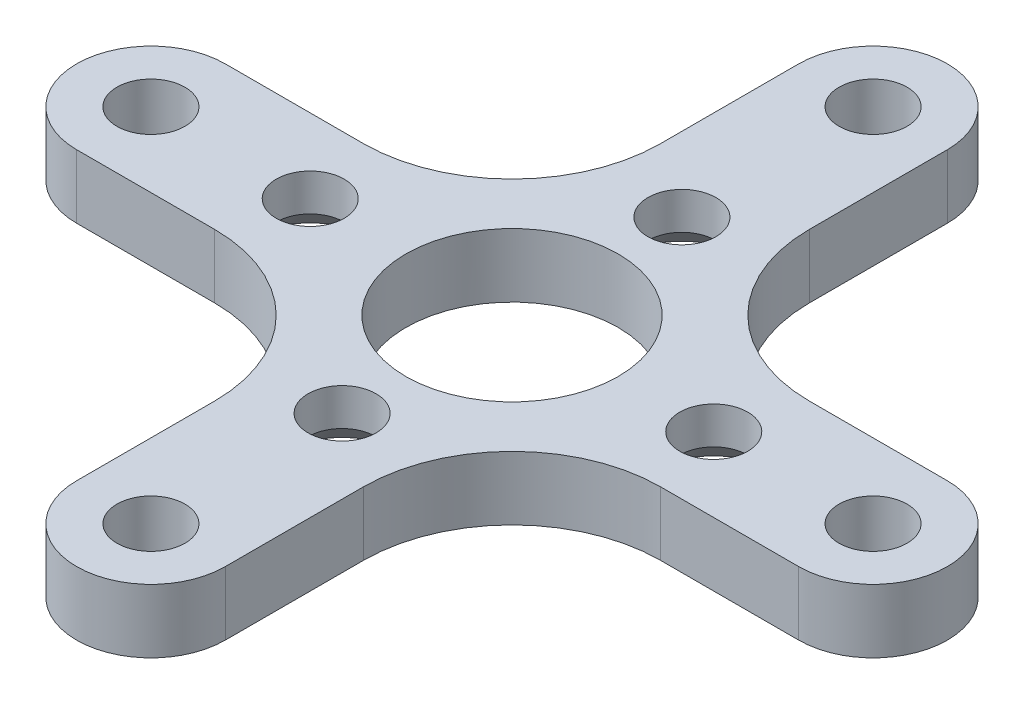
SolidWorks part; units mm, degrees
ref_plane "Front Plane" through (0, 0, 0) normal (0, 0, 1) x (1, 0, 0)
ref_plane "Top Plane" through (0, 0, 0) normal (0, 1, 0) x (1, 0, 0)
ref_plane "Right Plane" through (0, 0, 0) normal (1, 0, 0) x (0, 0, -1)
sketch "Sketch1" plane through (0, 0, 0) normal (0, 1, 0) x (1, 0, 0)
  line L0 (0, 69.7418) -> (0, -61.909) construction
  line L2 (3.5, -17) -> (3.5, -10.5)
  line L4 (-3.5, -17) -> (-3.5, -10.5)
  line L5 (-66.5785, 0) -> (62.9634, 0) construction
  line L6 (-3.5, 10.5) -> (-3.5, 17)
  line L7 (-17, 3.5) -> (-10.5, 3.5)
  line L9 (-17, -3.5) -> (-10.5, -3.5)
  line L11 (10.5, -3.5) -> (17, -3.5)
  line L12 (3.5, 10.5) -> (3.5, 17)
  line L13 (10.5, 3.5) -> (17, 3.5)
  arc A10 (-3.5, 10.5) -> (-10.5, 3.5) centre (-10.5, 10.5) cw
  arc A11 (-3.5, -10.5) -> (-10.5, -3.5) centre (-10.5, -10.5) ccw
  arc A12 (10.5, 3.5) -> (3.5, 10.5) centre (10.5, 10.5) cw
  arc A13 (3.5, -10.5) -> (10.5, -3.5) centre (10.5, -10.5) cw
  arc A15 (-16.6397, 3.4814) -> (-16.6397, -3.4814) centre (-17, 0) ccw
  arc A16 (3.4814, 16.6397) -> (-3.4814, 16.6397) centre (0, 17) ccw
  arc A17 (16.6397, -3.4814) -> (16.6397, 3.4814) centre (17, 0) ccw
  arc A18 (-3.4814, -16.6397) -> (3.4814, -16.6397) centre (0, -17) ccw
  point P30 (0, 0)
  point P61 (0, 0)
  dimension "D10" = 7
  dimension "D11" = 7
  dimension "D12" = 7
  dimension "D13" = 7
  dimension "D15" = 4
extrude "Boss-Extrude1" add sketch "Sketch1" along normal blind 3
sketch "Sketch2" plane through (0, 0, 0) normal (0, -1, 0) x (1, 0, 0)
  line L0 (20.5, 0) -> (-20.5, 0) construction
  line L1 (0, -20.5) -> (0, 20.5) construction
  arc A0 (-17, 3.5) -> (-17, -3.5) centre (-17, 0) ccw construction
  arc A1 (17, -3.5) -> (17, 3.5) centre (17, 0) ccw construction
  arc A2 (-3.5, -17) -> (3.5, -17) centre (0, -17) ccw construction
  arc A3 (3.5, 17) -> (-3.5, 17) centre (0, 17) ccw construction
  circle A4 centre (0, 0) radius 17 construction
  dimension "D1" = 34
hole_wizard "Ø10.0 (10) Diameter Hole1" positions "3DSketch4" profile "Sketch5" hole size "Ø10.0" standard "ISO"
sketch3d "3DSketch4"
  point P0 (0, 0, 0)
  point P3 (0, 0, 0)
sketch "Sketch5" plane through (0, 0, 0) normal (1, 0, 0) x (0, 0, -1)
  line L0 (0, 0) -> (0, 13.0043)
  line L1 (0, 13.0043) -> (5, 10)
  line L2 (5, 10) -> (5, 0)
  line L5 (5, 0) -> (0, 0)
  line L10 (0, 13.0043) -> (-5, 10) construction
  line L11 (0, -6.35) -> (0, 107.95) construction
  dimension "Hole Dia." = 10
  dimension "Hole Depth" = 10
  dimension "Drill Angle" = 118
hole_wizard "Ø3.2 (3.2) Diameter Hole3" positions "3DSketch7" profile "Sketch8" hole size "Ø3.2" standard "ISO"
sketch3d "3DSketch7"
  line L0 (0, 0, -20.5) -> (0, 0, 20.5) construction
  circle A0 centre (0, 0, 0) radius 17 construction
  point P0 (0, 0, 17)
  point P6 (0, -17, 0)
sketch "Sketch8" plane through (0, 0, 17) normal (1, 0, 0) x (0, 0, -1)
  line L0 (0, 0) -> (0, 10.9614)
  line L1 (0, 10.9614) -> (1.6, 10)
  line L2 (1.6, 10) -> (1.6, 0)
  line L5 (1.6, 0) -> (0, 0)
  line L10 (0, 10.9614) -> (-1.6, 10) construction
  line L11 (0, -6.35) -> (0, 107.95) construction
  dimension "Hole Dia." = 3.2
  dimension "Hole Depth" = 10
  dimension "Drill Angle" = 118
pattern_circular "CirPattern1" count 4 over 360 about axis through (0, 0, 0) along (0, 1, 0) of "Ø3.2 (3.2) Diameter Hole3"
hole_wizard "CSK for M3 Flat Head Machine Screw1" positions "3DSketch8" profile "Sketch9" countersink size "M3" standard "ANSI Metric" end condition through all
sketch3d "3DSketch8"
  line L0 (0, 0, -20.5) -> (0, 0, 20.5) construction
  line L1 (20.5, 0, 0) -> (-20.5, 0, 0) construction
  point P0 (0, 0, -8)
  point P4 (0, 0, 8)
  point P6 (-9.5, 0, 0)
  point P10 (9.5, 0, 0)
  dimension "D1" = 16
  dimension "D2" = 8
  dimension "D3" = 19
  dimension "D4" = 9.5
sketch "Sketch9" plane through (0, 0, -8) normal (1, 0, 0) x (0, 0, -1)
  line L0 (0, 0) -> (0, 3)
  line L1 (0, 3) -> (1.6, 3)
  line L2 (1.6, 3) -> (1.6, 1.25)
  line L3 (1.6, 1.25) -> (2.85, 0)
  line L5 (2.85, 0) -> (0, 0)
  line L6 (-1.6, 1.25) -> (-2.85, 0) construction
  line L11 (0, -6.35) -> (0, 107.95) construction
  dimension "Thru Hole Dia." = 3.2
  dimension "Thru Hole Depth" = 3
  dimension "Near C'Sink Dia." = 5.7
  dimension "Near C'Sink Angle" = 90
